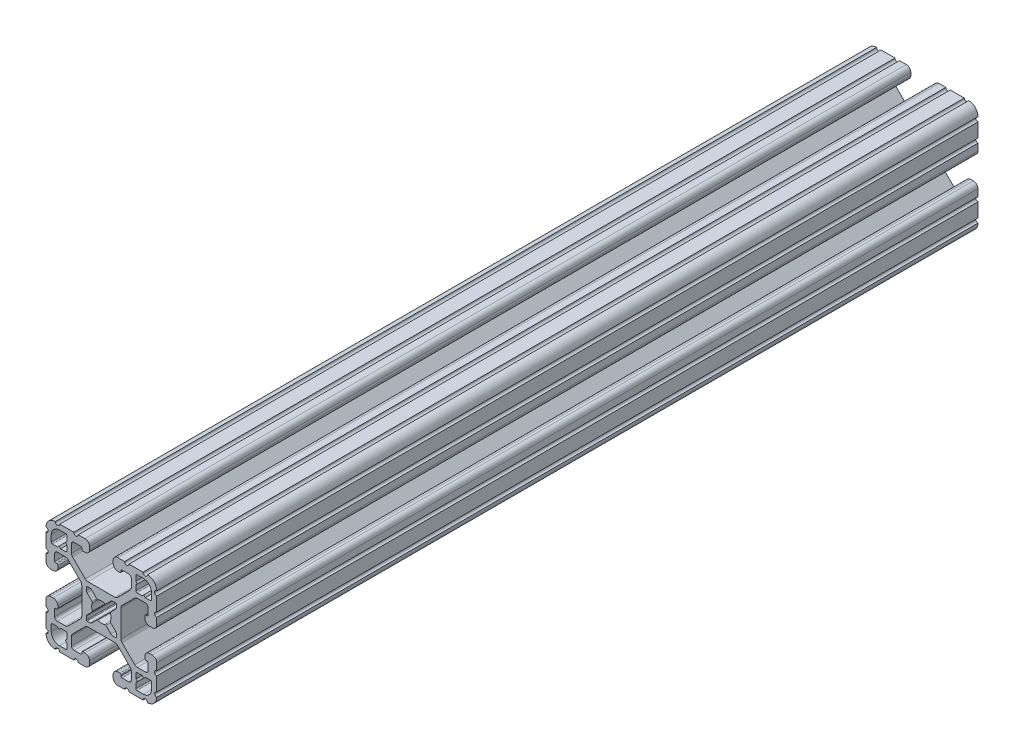
SolidWorks part; units mm, degrees
ref_plane "Front Plane" through (0, 0, 0) normal (0, 0, 1) x (1, 0, 0)
ref_plane "Top Plane" through (0, 0, 0) normal (0, 1, 0) x (1, 0, 0)
ref_plane "Right Plane" through (0, 0, 0) normal (1, 0, 0) x (0, 0, -1)
ref_plane "Plane1" through (0, 0, -2322.576) normal (0, 0, -1) x (-1, 0, 0)
sketch "Sketch1" plane through (0, 0, -2322.576) normal (0, 0, -1) x (-1, 0, 0)
  line L0 (17.2466, 14.4526) -> (17.2466, 12.2428)
  line L1 (16.8656, 11.8618) -> (15.0927, 11.8618)
  line L2 (15.0927, 11.8618) -> (14.5542, 12.4003)
  line L3 (14.5542, 12.4003) -> (14.0157, 11.8618)
  line L4 (14.0157, 11.8618) -> (12.2428, 11.8618)
  line L5 (11.8618, 12.2428) -> (11.8618, 14.0157)
  line L6 (11.8618, 14.0157) -> (12.4003, 14.5542)
  line L7 (12.4003, 14.5542) -> (11.8618, 15.0927)
  line L8 (11.8618, 15.0927) -> (11.8618, 16.8656)
  line L9 (12.2428, 17.2466) -> (14.4526, 17.2466)
  line L10 (17.2466, -12.2428) -> (17.2466, -14.4526)
  line L11 (14.4526, -17.2466) -> (12.2428, -17.2466)
  line L12 (11.8618, -16.8656) -> (11.8618, -15.0927)
  line L13 (11.8618, -15.0927) -> (12.4003, -14.5542)
  line L14 (12.4003, -14.5542) -> (11.8618, -14.0157)
  line L15 (11.8618, -14.0157) -> (11.8618, -12.2428)
  line L16 (12.2428, -11.8618) -> (14.0157, -11.8618)
  line L17 (14.0157, -11.8618) -> (14.5542, -12.4003)
  line L18 (14.5542, -12.4003) -> (15.0927, -11.8618)
  line L19 (15.0927, -11.8618) -> (16.8656, -11.8618)
  line L20 (5.1689, -3.9207) -> (5.1689, -4.9149)
  line L21 (4.9149, -5.1689) -> (3.9207, -5.1689)
  line L22 (3.2921, -4.9085) -> (1.5823, -3.1988)
  line L23 (-1.5823, -3.1988) -> (-3.2921, -4.9085)
  line L24 (-3.9207, -5.1689) -> (-4.9149, -5.1689)
  line L25 (-5.1689, -4.9149) -> (-5.1689, -3.9207)
  line L26 (-4.9085, -3.2921) -> (-3.1988, -1.5823)
  line L27 (-3.1988, 1.5823) -> (-4.9085, 3.2921)
  line L28 (-5.1689, 3.9207) -> (-5.1689, 4.9149)
  line L29 (-4.9149, 5.1689) -> (-3.9207, 5.1689)
  line L30 (-3.2921, 4.9085) -> (-1.5823, 3.1988)
  line L31 (1.5823, 3.1988) -> (3.2921, 4.9085)
  line L32 (3.9207, 5.1689) -> (4.9149, 5.1689)
  line L33 (5.1689, 4.9149) -> (5.1689, 3.9207)
  line L34 (4.9085, 3.2921) -> (3.1988, 1.5823)
  line L35 (3.1988, -1.5823) -> (4.9085, -3.2921)
  line L36 (-11.8618, -12.2428) -> (-11.8618, -14.0157)
  line L37 (-11.8618, -14.0157) -> (-12.4003, -14.5542)
  line L38 (-12.4003, -14.5542) -> (-11.8618, -15.0927)
  line L39 (-11.8618, -15.0927) -> (-11.8618, -16.8656)
  line L40 (-12.2428, -17.2466) -> (-14.4526, -17.2466)
  line L41 (-17.2466, -14.4526) -> (-17.2466, -12.2428)
  line L42 (-16.8656, -11.8618) -> (-15.0927, -11.8618)
  line L43 (-15.0927, -11.8618) -> (-14.5542, -12.4003)
  line L44 (-14.5542, -12.4003) -> (-14.0157, -11.8618)
  line L45 (-14.0157, -11.8618) -> (-12.2428, -11.8618)
  line L46 (-11.8618, 16.8656) -> (-11.8618, 15.0927)
  line L47 (-11.8618, 15.0927) -> (-12.4003, 14.5542)
  line L48 (-12.4003, 14.5542) -> (-11.8618, 14.0157)
  line L49 (-11.8618, 14.0157) -> (-11.8618, 12.2428)
  line L50 (-12.2428, 11.8618) -> (-14.0157, 11.8618)
  line L51 (-14.0157, 11.8618) -> (-14.5542, 12.4003)
  line L52 (-14.5542, 12.4003) -> (-15.0927, 11.8618)
  line L53 (-15.0927, 11.8618) -> (-16.8656, 11.8618)
  line L54 (-17.2466, 12.2428) -> (-17.2466, 14.4526)
  line L55 (-14.4526, 17.2466) -> (-12.2428, 17.2466)
  line L56 (19.05, -14.3256) -> (19.05, -9.4996)
  line L57 (19.05, -7.9756) -> (19.05, -5.6388)
  line L58 (17.4752, -4.064) -> (16.5608, -4.064)
  line L59 (14.986, -5.6388) -> (14.986, -6.35)
  line L60 (15.367, -6.731) -> (15.6972, -6.731)
  line L61 (16.0782, -7.112) -> (16.0782, -9.398)
  line L62 (15.1892, -10.287) -> (12.3756, -10.287)
  line L63 (11.4776, -9.915) -> (7.1157, -5.5531)
  line L64 (6.7437, -4.6551) -> (6.7437, 4.6551)
  line L65 (7.1157, 5.5531) -> (11.4776, 9.915)
  line L66 (12.3756, 10.287) -> (15.1892, 10.287)
  line L67 (16.0782, 9.398) -> (16.0782, 7.112)
  line L68 (15.6972, 6.731) -> (15.367, 6.731)
  line L69 (14.986, 6.35) -> (14.986, 5.6388)
  line L70 (16.5608, 4.064) -> (17.4752, 4.064)
  line L71 (19.05, 5.6388) -> (19.05, 7.9756)
  line L72 (19.05, 9.4996) -> (19.05, 14.3256)
  line L73 (14.3256, 19.05) -> (9.4996, 19.05)
  line L74 (7.9756, 19.05) -> (5.6388, 19.05)
  line L75 (4.064, 17.4752) -> (4.064, 16.5608)
  line L76 (5.6388, 14.986) -> (6.35, 14.986)
  line L77 (6.731, 15.367) -> (6.731, 15.6972)
  line L78 (7.112, 16.0782) -> (9.398, 16.0782)
  line L79 (10.287, 15.1892) -> (10.287, 12.3756)
  line L80 (9.915, 11.4776) -> (5.5531, 7.1157)
  line L81 (4.6551, 6.7437) -> (-4.6551, 6.7437)
  line L82 (-5.5531, 7.1157) -> (-9.915, 11.4776)
  line L83 (-10.287, 12.3756) -> (-10.287, 15.1892)
  line L84 (-9.398, 16.0782) -> (-7.112, 16.0782)
  line L85 (-6.731, 15.6972) -> (-6.731, 15.367)
  line L86 (-6.35, 14.986) -> (-5.6388, 14.986)
  line L87 (-4.064, 16.5608) -> (-4.064, 17.4752)
  line L88 (-5.6388, 19.05) -> (-7.9756, 19.05)
  line L89 (-9.4996, 19.05) -> (-14.3256, 19.05)
  line L90 (-19.05, 14.3256) -> (-19.05, 9.4996)
  line L91 (-19.05, 7.9756) -> (-19.05, 5.6388)
  line L92 (-17.4752, 4.064) -> (-16.5608, 4.064)
  line L93 (-14.986, 5.6388) -> (-14.986, 6.35)
  line L94 (-15.367, 6.731) -> (-15.6972, 6.731)
  line L95 (-16.0782, 7.112) -> (-16.0782, 9.398)
  line L96 (-15.1892, 10.287) -> (-12.3756, 10.287)
  line L97 (-11.4776, 9.915) -> (-7.1157, 5.5531)
  line L98 (-6.7437, 4.6551) -> (-6.7437, -4.6551)
  line L99 (-7.1157, -5.5531) -> (-11.4776, -9.915)
  line L100 (-12.3756, -10.287) -> (-15.1892, -10.287)
  line L101 (-16.0782, -9.398) -> (-16.0782, -7.112)
  line L102 (-15.6972, -6.731) -> (-15.367, -6.731)
  line L103 (-14.986, -6.35) -> (-14.986, -5.6388)
  line L104 (-16.5608, -4.064) -> (-17.4752, -4.064)
  line L105 (-19.05, -5.6388) -> (-19.05, -7.9756)
  line L106 (-19.05, -9.4996) -> (-19.05, -14.3256)
  line L107 (-14.3256, -19.05) -> (-9.4996, -19.05)
  line L108 (-7.9756, -19.05) -> (-5.6388, -19.05)
  line L109 (-4.064, -17.4752) -> (-4.064, -16.5608)
  line L110 (-5.6388, -14.986) -> (-6.35, -14.986)
  line L111 (-6.731, -15.367) -> (-6.731, -15.6972)
  line L112 (-7.112, -16.0782) -> (-9.398, -16.0782)
  line L113 (-10.287, -15.1892) -> (-10.287, -12.3756)
  line L114 (-9.915, -11.4776) -> (-5.5531, -7.1157)
  line L115 (-4.6551, -6.7437) -> (4.6551, -6.7437)
  line L116 (5.5531, -7.1157) -> (9.915, -11.4776)
  line L117 (10.287, -12.3756) -> (10.287, -15.1892)
  line L118 (9.398, -16.0782) -> (7.112, -16.0782)
  line L119 (6.731, -15.6972) -> (6.731, -15.367)
  line L120 (6.35, -14.986) -> (5.6388, -14.986)
  line L121 (4.064, -16.5608) -> (4.064, -17.4752)
  line L122 (5.6388, -19.05) -> (7.9756, -19.05)
  line L123 (9.4996, -19.05) -> (14.3256, -19.05)
  arc A0 (17.2466, 12.2428) -> (16.8656, 11.8618) centre (16.8656, 12.2428) cw
  arc A1 (12.2428, 11.8618) -> (11.8618, 12.2428) centre (12.2428, 12.2428) cw
  arc A2 (11.8618, 16.8656) -> (12.2428, 17.2466) centre (12.2428, 16.8656) cw
  arc A3 (14.4526, 17.2466) -> (17.2466, 14.4526) centre (14.4526, 14.4526) cw
  arc A4 (17.2466, -14.4526) -> (14.4526, -17.2466) centre (14.4526, -14.4526) cw
  arc A5 (12.2428, -17.2466) -> (11.8618, -16.8656) centre (12.2428, -16.8656) cw
  arc A6 (11.8618, -12.2428) -> (12.2428, -11.8618) centre (12.2428, -12.2428) cw
  arc A7 (16.8656, -11.8618) -> (17.2466, -12.2428) centre (16.8656, -12.2428) cw
  arc A8 (5.1689, -4.9149) -> (4.9149, -5.1689) centre (4.9149, -4.9149) cw
  arc A9 (3.9207, -5.1689) -> (3.2921, -4.9085) centre (3.9207, -4.2799) cw
  arc A10 (1.5823, -3.1988) -> (1.178, -3.1119) centre (1.3129, -3.4682) ccw
  arc A11 (1.178, -3.1119) -> (-1.178, -3.1119) centre (0, 0) cw
  arc A12 (-1.178, -3.1119) -> (-1.5823, -3.1988) centre (-1.3129, -3.4682) ccw
  arc A13 (-3.2921, -4.9085) -> (-3.9207, -5.1689) centre (-3.9207, -4.2799) cw
  arc A14 (-4.9149, -5.1689) -> (-5.1689, -4.9149) centre (-4.9149, -4.9149) cw
  arc A15 (-5.1689, -3.9207) -> (-4.9085, -3.2921) centre (-4.2799, -3.9207) cw
  arc A16 (-3.1988, -1.5823) -> (-3.1119, -1.178) centre (-3.4682, -1.3129) ccw
  arc A17 (-3.1119, -1.178) -> (-3.1119, 1.178) centre (0, 0) cw
  arc A18 (-3.1119, 1.178) -> (-3.1988, 1.5823) centre (-3.4682, 1.3129) ccw
  arc A19 (-4.9085, 3.2921) -> (-5.1689, 3.9207) centre (-4.2799, 3.9207) cw
  arc A20 (-5.1689, 4.9149) -> (-4.9149, 5.1689) centre (-4.9149, 4.9149) cw
  arc A21 (-3.9207, 5.1689) -> (-3.2921, 4.9085) centre (-3.9207, 4.2799) cw
  arc A22 (-1.5823, 3.1988) -> (-1.178, 3.1119) centre (-1.3129, 3.4682) ccw
  arc A23 (-1.178, 3.1119) -> (1.178, 3.1119) centre (0, 0) cw
  arc A24 (1.178, 3.1119) -> (1.5823, 3.1988) centre (1.3129, 3.4682) ccw
  arc A25 (3.2921, 4.9085) -> (3.9207, 5.1689) centre (3.9207, 4.2799) cw
  arc A26 (4.9149, 5.1689) -> (5.1689, 4.9149) centre (4.9149, 4.9149) cw
  arc A27 (5.1689, 3.9207) -> (4.9085, 3.2921) centre (4.2799, 3.9207) cw
  arc A28 (3.1988, 1.5823) -> (3.1119, 1.178) centre (3.4682, 1.3129) ccw
  arc A29 (3.1119, 1.178) -> (3.1119, -1.178) centre (0, 0) cw
  arc A30 (3.1119, -1.178) -> (3.1988, -1.5823) centre (3.4682, -1.3129) ccw
  arc A31 (4.9085, -3.2921) -> (5.1689, -3.9207) centre (4.2799, -3.9207) cw
  arc A32 (-11.8618, -16.8656) -> (-12.2428, -17.2466) centre (-12.2428, -16.8656) cw
  arc A33 (-14.4526, -17.2466) -> (-17.2466, -14.4526) centre (-14.4526, -14.4526) cw
  arc A34 (-17.2466, -12.2428) -> (-16.8656, -11.8618) centre (-16.8656, -12.2428) cw
  arc A35 (-12.2428, -11.8618) -> (-11.8618, -12.2428) centre (-12.2428, -12.2428) cw
  arc A36 (-12.2428, 17.2466) -> (-11.8618, 16.8656) centre (-12.2428, 16.8656) cw
  arc A37 (-11.8618, 12.2428) -> (-12.2428, 11.8618) centre (-12.2428, 12.2428) cw
  arc A38 (-16.8656, 11.8618) -> (-17.2466, 12.2428) centre (-16.8656, 12.2428) cw
  arc A39 (-17.2466, 14.4526) -> (-14.4526, 17.2466) centre (-14.4526, 14.4526) cw
  arc A40 (19.05, -9.4996) -> (19.05, -7.9756) centre (19.05, -8.7376) cw
  arc A41 (19.05, -5.6388) -> (17.4752, -4.064) centre (17.4752, -5.6388) ccw
  arc A42 (16.5608, -4.064) -> (14.986, -5.6388) centre (16.5608, -5.6388) ccw
  arc A43 (14.986, -6.35) -> (15.367, -6.731) centre (15.367, -6.35) ccw
  arc A44 (15.6972, -6.731) -> (16.0782, -7.112) centre (15.6972, -7.112) cw
  arc A45 (16.0782, -9.398) -> (15.1892, -10.287) centre (15.1892, -9.398) cw
  arc A46 (12.3756, -10.287) -> (11.4776, -9.915) centre (12.3756, -9.017) cw
  arc A47 (7.1157, -5.5531) -> (6.7437, -4.6551) centre (8.0137, -4.6551) cw
  arc A48 (6.7437, 4.6551) -> (7.1157, 5.5531) centre (8.0137, 4.6551) cw
  arc A49 (11.4776, 9.915) -> (12.3756, 10.287) centre (12.3756, 9.017) cw
  arc A50 (15.1892, 10.287) -> (16.0782, 9.398) centre (15.1892, 9.398) cw
  arc A51 (16.0782, 7.112) -> (15.6972, 6.731) centre (15.6972, 7.112) cw
  arc A52 (15.367, 6.731) -> (14.986, 6.35) centre (15.367, 6.35) ccw
  arc A53 (14.986, 5.6388) -> (16.5608, 4.064) centre (16.5608, 5.6388) ccw
  arc A54 (17.4752, 4.064) -> (19.05, 5.6388) centre (17.4752, 5.6388) ccw
  arc A55 (19.05, 7.9756) -> (19.05, 9.4996) centre (19.05, 8.7376) cw
  arc A56 (19.05, 14.3256) -> (19.0499, 15.8496) centre (19.05, 15.0876) cw
  arc A57 (19.0499, 15.8496) -> (15.8496, 19.0499) centre (15.875, 15.875) ccw
  arc A58 (15.8496, 19.0499) -> (14.3256, 19.05) centre (15.0876, 19.05) cw
  arc A59 (9.4996, 19.05) -> (7.9756, 19.05) centre (8.7376, 19.05) cw
  arc A60 (5.6388, 19.05) -> (4.064, 17.4752) centre (5.6388, 17.4752) ccw
  arc A61 (4.064, 16.5608) -> (5.6388, 14.986) centre (5.6388, 16.5608) ccw
  arc A62 (6.35, 14.986) -> (6.731, 15.367) centre (6.35, 15.367) ccw
  arc A63 (6.731, 15.6972) -> (7.112, 16.0782) centre (7.112, 15.6972) cw
  arc A64 (9.398, 16.0782) -> (10.287, 15.1892) centre (9.398, 15.1892) cw
  arc A65 (10.287, 12.3756) -> (9.915, 11.4776) centre (9.017, 12.3756) cw
  arc A66 (5.5531, 7.1157) -> (4.6551, 6.7437) centre (4.6551, 8.0137) cw
  arc A67 (-4.6551, 6.7437) -> (-5.5531, 7.1157) centre (-4.6551, 8.0137) cw
  arc A68 (-9.915, 11.4776) -> (-10.287, 12.3756) centre (-9.017, 12.3756) cw
  arc A69 (-10.287, 15.1892) -> (-9.398, 16.0782) centre (-9.398, 15.1892) cw
  arc A70 (-7.112, 16.0782) -> (-6.731, 15.6972) centre (-7.112, 15.6972) cw
  arc A71 (-6.731, 15.367) -> (-6.35, 14.986) centre (-6.35, 15.367) ccw
  arc A72 (-5.6388, 14.986) -> (-4.064, 16.5608) centre (-5.6388, 16.5608) ccw
  arc A73 (-4.064, 17.4752) -> (-5.6388, 19.05) centre (-5.6388, 17.4752) ccw
  arc A74 (-7.9756, 19.05) -> (-9.4996, 19.05) centre (-8.7376, 19.05) cw
  arc A75 (-14.3256, 19.05) -> (-15.8496, 19.0499) centre (-15.0876, 19.05) cw
  arc A76 (-15.8496, 19.0499) -> (-19.0499, 15.8496) centre (-15.875, 15.875) ccw
  arc A77 (-19.0499, 15.8496) -> (-19.05, 14.3256) centre (-19.05, 15.0876) cw
  arc A78 (-19.05, 9.4996) -> (-19.05, 7.9756) centre (-19.05, 8.7376) cw
  arc A79 (-19.05, 5.6388) -> (-17.4752, 4.064) centre (-17.4752, 5.6388) ccw
  arc A80 (-16.5608, 4.064) -> (-14.986, 5.6388) centre (-16.5608, 5.6388) ccw
  arc A81 (-14.986, 6.35) -> (-15.367, 6.731) centre (-15.367, 6.35) ccw
  arc A82 (-15.6972, 6.731) -> (-16.0782, 7.112) centre (-15.6972, 7.112) cw
  arc A83 (-16.0782, 9.398) -> (-15.1892, 10.287) centre (-15.1892, 9.398) cw
  arc A84 (-12.3756, 10.287) -> (-11.4776, 9.915) centre (-12.3756, 9.017) cw
  arc A85 (-7.1157, 5.5531) -> (-6.7437, 4.6551) centre (-8.0137, 4.6551) cw
  arc A86 (-6.7437, -4.6551) -> (-7.1157, -5.5531) centre (-8.0137, -4.6551) cw
  arc A87 (-11.4776, -9.915) -> (-12.3756, -10.287) centre (-12.3756, -9.017) cw
  arc A88 (-15.1892, -10.287) -> (-16.0782, -9.398) centre (-15.1892, -9.398) cw
  arc A89 (-16.0782, -7.112) -> (-15.6972, -6.731) centre (-15.6972, -7.112) cw
  arc A90 (-15.367, -6.731) -> (-14.986, -6.35) centre (-15.367, -6.35) ccw
  arc A91 (-14.986, -5.6388) -> (-16.5608, -4.064) centre (-16.5608, -5.6388) ccw
  arc A92 (-17.4752, -4.064) -> (-19.05, -5.6388) centre (-17.4752, -5.6388) ccw
  arc A93 (-19.05, -7.9756) -> (-19.05, -9.4996) centre (-19.05, -8.7376) cw
  arc A94 (-19.05, -14.3256) -> (-19.0499, -15.8496) centre (-19.05, -15.0876) cw
  arc A95 (-19.0499, -15.8496) -> (-15.8496, -19.0499) centre (-15.875, -15.875) ccw
  arc A96 (-15.8496, -19.0499) -> (-14.3256, -19.05) centre (-15.0876, -19.05) cw
  arc A97 (-9.4996, -19.05) -> (-7.9756, -19.05) centre (-8.7376, -19.05) cw
  arc A98 (-5.6388, -19.05) -> (-4.064, -17.4752) centre (-5.6388, -17.4752) ccw
  arc A99 (-4.064, -16.5608) -> (-5.6388, -14.986) centre (-5.6388, -16.5608) ccw
  arc A100 (-6.35, -14.986) -> (-6.731, -15.367) centre (-6.35, -15.367) ccw
  arc A101 (-6.731, -15.6972) -> (-7.112, -16.0782) centre (-7.112, -15.6972) cw
  arc A102 (-9.398, -16.0782) -> (-10.287, -15.1892) centre (-9.398, -15.1892) cw
  arc A103 (-10.287, -12.3756) -> (-9.915, -11.4776) centre (-9.017, -12.3756) cw
  arc A104 (-5.5531, -7.1157) -> (-4.6551, -6.7437) centre (-4.6551, -8.0137) cw
  arc A105 (4.6551, -6.7437) -> (5.5531, -7.1157) centre (4.6551, -8.0137) cw
  arc A106 (9.915, -11.4776) -> (10.287, -12.3756) centre (9.017, -12.3756) cw
  arc A107 (10.287, -15.1892) -> (9.398, -16.0782) centre (9.398, -15.1892) cw
  arc A108 (7.112, -16.0782) -> (6.731, -15.6972) centre (7.112, -15.6972) cw
  arc A109 (6.731, -15.367) -> (6.35, -14.986) centre (6.35, -15.367) ccw
  arc A110 (5.6388, -14.986) -> (4.064, -16.5608) centre (5.6388, -16.5608) ccw
  arc A111 (4.064, -17.4752) -> (5.6388, -19.05) centre (5.6388, -17.4752) ccw
  arc A112 (7.9756, -19.05) -> (9.4996, -19.05) centre (8.7376, -19.05) cw
  arc A113 (14.3256, -19.05) -> (15.8496, -19.0499) centre (15.0876, -19.05) cw
  arc A114 (15.8496, -19.0499) -> (19.0499, -15.8496) centre (15.875, -15.875) ccw
  arc A115 (19.0499, -15.8496) -> (19.05, -14.3256) centre (19.05, -15.0876) cw
extrude "Boss-Extrude1" add sketch "Sketch1" against normal blind 282.575
